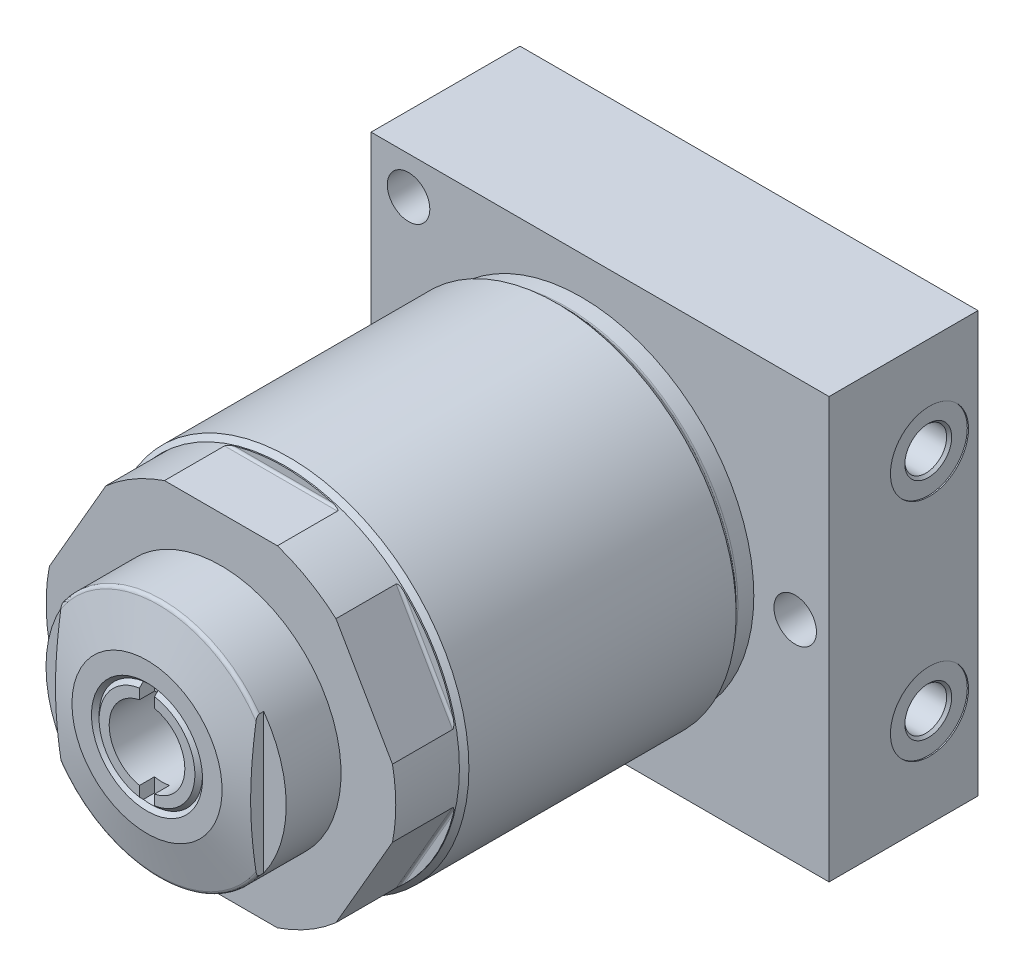
SolidWorks part; units mm, degrees
material "Alloy Steel"
ref_plane "Front Plane" through (0, 0, 0) normal (0, 0, 1) x (1, 0, 0)
ref_plane "Top Plane" through (0, 0, 0) normal (0, 1, 0) x (1, 0, 0)
ref_plane "Right Plane" through (0, 0, 0) normal (1, 0, 0) x (0, 0, -1)
sketch "Sketch1" plane through (0, 0, 0) normal (1, 0, 0) x (0, 0, -1)
  line L0 (0, 0) -> (122.3375, 0) construction
  line L1 (0, 0) -> (0, 13.9954)
  line L2 (0, 13.9954) -> (-4.6736, 13.9954)
  line L3 (-4.6736, 13.9954) -> (-4.6736, 36.487)
  line L6 (-4.6736, 36.487) -> (-24.003, 36.487)
  line L7 (-24.6496, 36.7548) -> (-25.8678, 37.973)
  line L8 (-25.8678, 37.973) -> (-82.3845, 37.973)
  line L9 (-82.3845, 37.973) -> (-83.388, 36.9695)
  line L10 (-83.388, 36.9695) -> (-96.85, 36.9695)
  line L11 (-96.85, 36.9695) -> (-96.85, 0)
  line L12 (0, 0) -> (-96.85, 0)
  arc A0 (-24.003, 36.487) -> (-24.6496, 36.7548) centre (-24.003, 37.4014) cw
  dimension "D3" = 0.9144
  dimension "D1" = 27.9908
  dimension "D2" = 4.6736
  dimension "D4" = 24.003
  dimension "D5" = 72.974
  dimension "D7" = 75.946
  dimension "D8" = 45
  dimension "D9" = 96.85
  dimension "D10" = 73.939
  dimension "D11" = 45
  dimension "D12" = 13.462
revolve "Revolve1" add sketch "Sketch1" angle 360 about L0
sketch "Sketch2" plane through (0, 0, 0) normal (1, 0, 0) x (0, 0, -1)
  line L0 (0, 0) -> (-47.105, 0) construction
  line L1 (-96.85, 34.9885) -> (-84.15, 34.9885)
  line L2 (-96.85, 36.9695) -> (-96.85, -36.9695) construction
  line L3 (-83.642, 35.4965) -> (-83.642, 38.1635)
  line L4 (-83.642, 38.1635) -> (-96.85, 38.1635)
  line L5 (-96.85, 38.1635) -> (-96.85, 34.9885)
  arc A0 (-83.642, 35.4965) -> (-84.15, 34.9885) centre (-84.15, 35.4965) cw
  dimension "D4" = 0.508
  dimension "D1" = 69.977
  dimension "D2" = 13.208
  dimension "D3" = 3.175
extrude "Cut-Extrude1" cut sketch "Sketch2" against normal through all and the other way through all
pattern_circular "CirPattern1" count 6 over 360 about axis through (0, 0, 0) along (0, 0, 1) of "Cut-Extrude1"
sketch "Sketch6" plane through (0, 0, 0) normal (0, 1, 0) x (1, 0, 0)
  line L0 (-44.45, -20.65) -> (52.4, -20.65)
  line L1 (52.4, -20.65) -> (52.4, 10.846)
  line L2 (52.4, 10.846) -> (-44.45, 10.846)
  line L3 (-44.45, 10.846) -> (-44.45, -20.65)
  line L4 (11.9394, -96.85) -> (-11.9394, -96.85) construction
  dimension "D1" = 76.2
  dimension "D2" = 90
  dimension "D3" = 31.496
  dimension "D4" = 96.85
  dimension "D5" = 44.45
extrude "Extrude1" add sketch "Sketch6" along normal mid plane 88.9
sketch "Sketch3" plane through (0, 0, 0) normal (1, 0, 0) x (0, 0, -1)
  line L0 (0, 0) -> (-60.8041, 0) construction
  line L1 (-112.484, 0) -> (-112.484, 15.875)
  line L2 (-109.309, 25.4) -> (-96.85, 25.4)
  line L3 (-96.85, 7.1544) -> (-96.85, 27.8341) construction
  line L4 (-96.85, 25.4) -> (-96.85, 0)
  line L5 (-96.85, 7.1544) -> (-96.85, -7.1544) construction
  line L6 (-96.85, 0) -> (-112.484, 0)
  line L8 (-112.484, 15.875) -> (-110.0688, 24.8182)
  line L9 (10.846, 44.45) -> (10.846, -44.45) construction
  arc A0 (-109.309, 25.4) -> (-110.0688, 24.8182) centre (-109.309, 24.613) ccw
  dimension "D1" = 0.787
  dimension "D2" = 50.8
  dimension "D3" = 123.33
  dimension "D4" = 3.175
  dimension "D5" = 31.75
revolve "Revolve2" add sketch "Sketch3" angle 360 about L0
sketch "Sketch4" plane through (0, 0, 112.484) normal (0, 0, 1) x (1, 0, 0)
  circle A0 centre (0, 0) radius 8.001
  circle A1 centre (0, 0) radius 25.4 construction
  dimension "D1" = 16.002
extrude "Cut-Extrude2" cut sketch "Sketch4" against normal blind 22.098
hole_wizard "Hole1" positions "Sketch8" profile "Sketch7" legacy end condition up to next
sketch "Sketch8" plane through (0, 0, 20.65) normal (0, 0, 1) x (1, 0, 0)
  line L0 (0, 0) -> (0, 25.169) construction
  line L1 (0, 0) -> (-25.7102, 0) construction
  point P0 (-36.5252, 36.5252)
  point P9 (-36.5252, -36.5252)
  point P10 (45.2374, 0)
  dimension "D1" = 36.5252
  dimension "D2" = 36.5252
  dimension "D3" = 45.2374
sketch "Sketch7" plane through (-36.5252, 36.5252, 20.65) normal (1, 0, 0) x (0, -1, 0)
  line L0 (0, 0) -> (0, 31.496)
  line L1 (0, 31.496) -> (4.496, 31.496)
  line L2 (4.496, 31.496) -> (4.496, 0)
  line L3 (4.496, 0) -> (0, 0)
  line L4 (0, 110) -> (0, -10) construction
  dimension "Diameter" = 8.992
  dimension "Depth" = 31.496
ref_plane "Plane1" through (0, -23.813, 0) normal (0, 1, 0) x (-1, 0, 0)
sketch "Sketch9" plane through (0, -23.813, 0) normal (0, 1, 0) x (-1, 0, 0)
  line L0 (-52.4, -0.585) -> (-18.7621, -0.585) construction
  line L1 (-52.4, 20.65) -> (-52.4, -10.846) construction
  line L2 (-52.4, 7.67) -> (-52.146, 7.67)
  line L3 (-52.146, 7.67) -> (-52.146, 4.368)
  line L4 (-52.146, 4.368) -> (-51.6126, 3.8346)
  line L5 (-51.6126, 3.8346) -> (-41.5796, 3.8346)
  line L6 (-41.5796, 3.8346) -> (-41.5796, -0.585)
  line L7 (-41.5796, -0.585) -> (-52.4, -0.585)
  line L8 (-52.4, -0.585) -> (-52.4, 7.67)
  dimension "D1" = 10.261
  dimension "D2" = 16.51
  dimension "D3" = 0.254
  dimension "D4" = 8.8392
  dimension "D5" = 10.5664
  dimension "D6" = 45
  dimension "D7" = 9.906
revolve "Cut-Revolve2" cut sketch "Sketch9" angle 360 about L0
pattern_linear "LPattern1" count 2 spacing 47.626 along (0, 1, 0) of "Cut-Revolve2"
sketch "Sketch12" plane through (0, 0, 0) normal (0, 1, 0) x (0, 0, -1)
  line L0 (0, 0) -> (-132.5997, 0) construction
  line L1 (-112.484, 15.875) -> (-112.484, -15.875) construction
  line L2 (-118.445, 30.6375) -> (-108.445, 30.6375)
  line L3 (-118.445, 30.6375) -> (-118.445, 20.6375)
  line L4 (-118.445, 20.6375) -> (-108.445, 20.6375)
  line L5 (-108.445, 30.6375) -> (-108.445, 20.6375)
  line L6 (-108.445, -30.6375) -> (-108.445, -20.6375)
  line L7 (-118.445, -20.6375) -> (-108.445, -20.6375)
  line L8 (-118.445, -30.6375) -> (-118.445, -20.6375)
  line L9 (-118.445, -30.6375) -> (-108.445, -30.6375)
  dimension "D1" = 41.275
  dimension "D2" = 4.039
  dimension "D3" = 10
  dimension "D4" = 10
extrude "Cut-Extrude3" cut sketch "Sketch12" against normal through all and the other way through all
sketch "Sketch13" plane through (0, 0, 0) normal (1, 0, 0) x (0, 0, -1)
  line L0 (0, 0) -> (-158.8154, 0) construction
  line L1 (-112.484, 11.7475) -> (-111.671, 10.9345)
  line L2 (-112.484, 15.875) -> (-112.484, -15.875) construction
  line L3 (-111.671, 10.9345) -> (-112.484, 10.1215)
  line L4 (-112.484, 10.1215) -> (-112.484, 11.7475)
  dimension "D1" = 45
  dimension "D2" = 0.813
  dimension "D3" = 10.9345
revolve "Cut-Revolve4" cut sketch "Sketch13" angle 360 about L0
sketch "Sketch14" plane through (0, 0, 112.484) normal (0, 0, 1) x (1, 0, 0)
  line L0 (0, 0) -> (0, 31.3543) construction
  line L1 (-1.5875, -10.8186) -> (-1.5875, 10.8186)
  line L2 (1.5875, -10.8186) -> (1.5875, 10.8186)
  circle A0 centre (0, 0) radius 10.9345 construction
  arc A1 (1.5875, 10.8186) -> (-1.5875, 10.8186) centre (0, 0) ccw
  arc A2 (-1.5875, -10.8186) -> (1.5875, -10.8186) centre (0, 0) ccw
  dimension "D1" = 3.175
extrude "Cut-Extrude4" cut sketch "Sketch14" against normal blind 3.175
